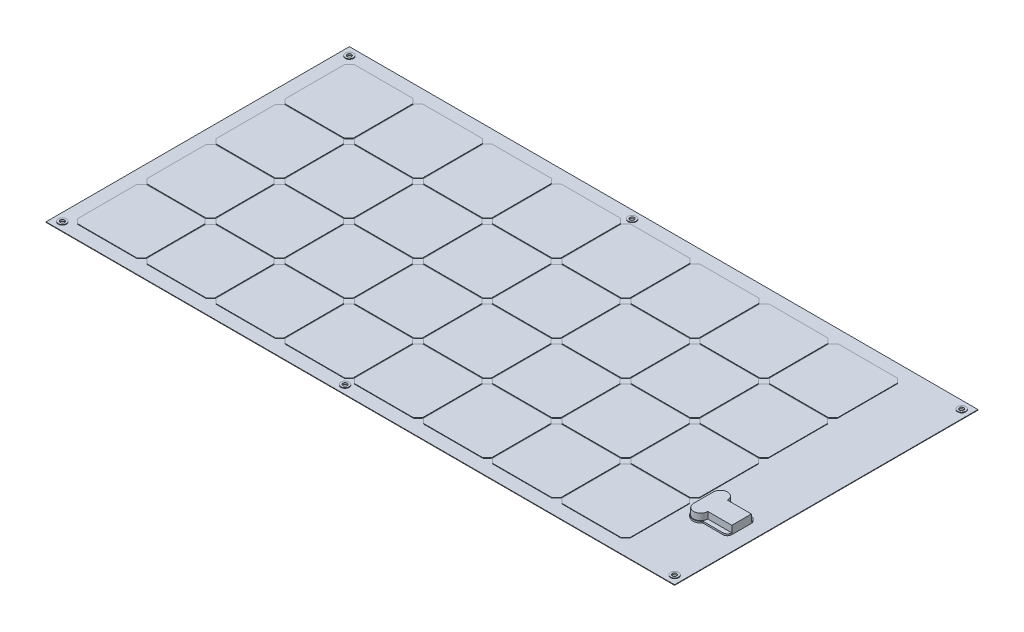
SolidWorks part; units mm, degrees
ref_plane "Front Plane" through (0, 0, 0) normal (0, 0, 1) x (1, 0, 0)
ref_plane "Top Plane" through (0, 0, 0) normal (0, 1, 0) x (1, 0, 0)
ref_plane "Right Plane" through (0, 0, 0) normal (1, 0, 0) x (0, 0, -1)
sketch "Sketch1" plane through (0, 0, 0) normal (0, 1, 0) x (1, 0, 0)
  line L1 (-577, 278.5) -> (577, 278.5)
  line L2 (-577, 278.5) -> (-577, -278.5)
  line L3 (-577, -278.5) -> (577, -278.5)
  line L4 (577, 278.5) -> (577, -278.5)
  line L5 (-577, 278.5) -> (577, -278.5) construction
  line L6 (-577, -278.5) -> (577, 278.5) construction
  point P0 (0, 0)
  dimension "D1" = 557
  dimension "D2" = 1154
extrude "Boss-Extrude1" add sketch "Sketch1" along normal blind 1
sketch "Sketch2" plane through (0, 1, 0) normal (0, 1, 0) x (1, 0, 0)
  line L0 (-577, 0) -> (577, 0) construction
  line L1 (-577, 278.5) -> (-577, -278.5) construction
  line L2 (577, -278.5) -> (577, 278.5) construction
  line L3 (-577, -278.5) -> (577, -278.5) construction
  circle A0 centre (-562, -263.5) radius 4
  circle A1 centre (-43, -263.5) radius 4
  circle A2 centre (562, -263.5) radius 4
  circle A3 centre (562, 263.5) radius 4
  circle A4 centre (-43, 263.5) radius 4
  circle A5 centre (-562, 263.5) radius 4
  dimension "D3" = 8
  dimension "D4" = 8
  dimension "D7" = 8
  dimension "D1" = 15
  dimension "D2" = 15
  dimension "D5" = 519
  dimension "D6" = 15
  dimension "D8" = 15
  dimension "D9" = 15
extrude "Cut-Extrude1" cut sketch "Sketch2" against normal blind 3
sketch "Sketch3" plane through (0, 1, 0) normal (0, 1, 0) x (1, 0, 0)
  line L0 (-552, -136.5) -> (-544, -128.5)
  line L1 (-544, -128.5) -> (-435, -128.5)
  line L2 (-552, -136.5) -> (-552, -245.5)
  line L3 (-544, -253.5) -> (-435, -253.5)
  line L4 (-427, -136.5) -> (-427, -245.5)
  line L5 (-552, -136.5) -> (-427, -136.5) construction
  line L6 (-552, -245.5) -> (-427, -245.5) construction
  line L7 (-435, -128.5) -> (-427, -136.5)
  line L8 (-435, -253.5) -> (-427, -245.5)
  line L9 (-552, -245.5) -> (-544, -253.5)
  line L10 (-544, -128.5) -> (-544, -253.5) construction
  line L11 (-435, -128.5) -> (-435, -253.5) construction
  line L12 (-577, 278.5) -> (-577, -278.5) construction
  line L13 (-577, -278.5) -> (577, -278.5) construction
  line L14 (-552, -9.5) -> (-544, -1.5)
  line L15 (-544, -1.5) -> (-435, -1.5)
  line L16 (-552, -9.5) -> (-552, -118.5)
  line L17 (-544, -126.5) -> (-435, -126.5)
  line L18 (-427, -9.5) -> (-427, -118.5)
  line L19 (-552, -9.5) -> (-427, -9.5) construction
  line L20 (-552, -118.5) -> (-427, -118.5) construction
  line L21 (-435, -1.5) -> (-427, -9.5)
  line L22 (-435, -126.5) -> (-427, -118.5)
  line L23 (-552, -118.5) -> (-544, -126.5)
  line L24 (-544, -1.5) -> (-544, -126.5) construction
  line L25 (-435, -1.5) -> (-435, -126.5) construction
  line L26 (-552, 117.5) -> (-544, 125.5)
  line L27 (-544, 125.5) -> (-435, 125.5)
  line L28 (-552, 117.5) -> (-552, 8.5)
  line L29 (-544, 0.5) -> (-435, 0.5)
  line L30 (-427, 117.5) -> (-427, 8.5)
  line L31 (-552, 117.5) -> (-427, 117.5) construction
  line L32 (-552, 8.5) -> (-427, 8.5) construction
  line L33 (-435, 125.5) -> (-427, 117.5)
  line L34 (-435, 0.5) -> (-427, 8.5)
  line L35 (-552, 8.5) -> (-544, 0.5)
  line L36 (-544, 125.5) -> (-544, 0.5) construction
  line L37 (-435, 125.5) -> (-435, 0.5) construction
  line L38 (-552, 245.5) -> (-544, 253.5)
  line L39 (-544, 253.5) -> (-435, 253.5)
  line L40 (-552, 245.5) -> (-552, 135.5)
  line L41 (-544, 127.5) -> (-435, 127.5)
  line L42 (-427, 245.5) -> (-427, 135.5)
  line L43 (-552, 245.5) -> (-427, 245.5) construction
  line L44 (-552, 135.5) -> (-427, 135.5) construction
  line L45 (-435, 253.5) -> (-427, 245.5)
  line L46 (-435, 127.5) -> (-427, 135.5)
  line L47 (-552, 135.5) -> (-544, 127.5)
  line L48 (-544, 253.5) -> (-544, 127.5) construction
  line L49 (-435, 253.5) -> (-435, 127.5) construction
  line L50 (577, 278.5) -> (-577, 278.5) construction
  line L51 (-426, 278.5) -> (-426, -278.5) construction
  line L52 (-417, 253.5) -> (-417, 127.5) construction
  line L53 (-308, 253.5) -> (-308, 127.5) construction
  line L54 (-300, 135.5) -> (-425, 135.5) construction
  line L55 (-300, 245.5) -> (-425, 245.5) construction
  line L56 (-417, 125.5) -> (-417, 0.5) construction
  line L57 (-308, 125.5) -> (-308, 0.5) construction
  line L58 (-300, 8.5) -> (-425, 8.5) construction
  line L59 (-300, 117.5) -> (-425, 117.5) construction
  line L60 (-417, -1.5) -> (-417, -126.5) construction
  line L61 (-308, -1.5) -> (-308, -126.5) construction
  line L62 (-300, -118.5) -> (-425, -118.5) construction
  line L63 (-300, -9.5) -> (-425, -9.5) construction
  line L64 (-417, -128.5) -> (-417, -253.5) construction
  line L65 (-308, -128.5) -> (-308, -253.5) construction
  line L66 (-300, -245.5) -> (-425, -245.5) construction
  line L67 (-300, -136.5) -> (-425, -136.5) construction
  line L68 (-300, 135.5) -> (-308, 127.5)
  line L69 (-417, 127.5) -> (-425, 135.5)
  line L70 (-417, 253.5) -> (-425, 245.5)
  line L71 (-425, 245.5) -> (-425, 135.5)
  line L72 (-308, 127.5) -> (-417, 127.5)
  line L73 (-300, 245.5) -> (-300, 135.5)
  line L74 (-308, 253.5) -> (-417, 253.5)
  line L75 (-300, 245.5) -> (-308, 253.5)
  line L76 (-300, 8.5) -> (-308, 0.5)
  line L77 (-417, 0.5) -> (-425, 8.5)
  line L78 (-417, 125.5) -> (-425, 117.5)
  line L79 (-425, 117.5) -> (-425, 8.5)
  line L80 (-308, 0.5) -> (-417, 0.5)
  line L81 (-300, 117.5) -> (-300, 8.5)
  line L82 (-308, 125.5) -> (-417, 125.5)
  line L83 (-300, 117.5) -> (-308, 125.5)
  line L84 (-300, -118.5) -> (-308, -126.5)
  line L85 (-417, -126.5) -> (-425, -118.5)
  line L86 (-417, -1.5) -> (-425, -9.5)
  line L87 (-425, -9.5) -> (-425, -118.5)
  line L88 (-308, -126.5) -> (-417, -126.5)
  line L89 (-300, -9.5) -> (-300, -118.5)
  line L90 (-308, -1.5) -> (-417, -1.5)
  line L91 (-300, -9.5) -> (-308, -1.5)
  line L92 (-300, -245.5) -> (-308, -253.5)
  line L93 (-417, -253.5) -> (-425, -245.5)
  line L94 (-417, -128.5) -> (-425, -136.5)
  line L95 (-425, -136.5) -> (-425, -245.5)
  line L96 (-308, -253.5) -> (-417, -253.5)
  line L97 (-300, -136.5) -> (-300, -245.5)
  line L98 (-308, -128.5) -> (-417, -128.5)
  line L99 (-300, -136.5) -> (-308, -128.5)
  line L100 (-299, 278.5) -> (-299, -278.5) construction
  line L101 (-298, -136.5) -> (-173, -136.5) construction
  line L102 (-298, -245.5) -> (-173, -245.5) construction
  line L103 (-290, -128.5) -> (-290, -253.5) construction
  line L104 (-181, -128.5) -> (-181, -253.5) construction
  line L105 (-298, -9.5) -> (-173, -9.5) construction
  line L106 (-298, -118.5) -> (-173, -118.5) construction
  line L107 (-290, -1.5) -> (-290, -126.5) construction
  line L108 (-181, -1.5) -> (-181, -126.5) construction
  line L109 (-298, 117.5) -> (-173, 117.5) construction
  line L110 (-298, 8.5) -> (-173, 8.5) construction
  line L111 (-290, 125.5) -> (-290, 0.5) construction
  line L112 (-181, 125.5) -> (-181, 0.5) construction
  line L113 (-298, 245.5) -> (-173, 245.5) construction
  line L114 (-298, 135.5) -> (-173, 135.5) construction
  line L115 (-290, 253.5) -> (-290, 127.5) construction
  line L116 (-181, 253.5) -> (-181, 127.5) construction
  line L117 (-163, 253.5) -> (-163, 127.5) construction
  line L118 (-54, 253.5) -> (-54, 127.5) construction
  line L119 (-46, 135.5) -> (-171, 135.5) construction
  line L120 (-46, 245.5) -> (-171, 245.5) construction
  line L121 (-163, 125.5) -> (-163, 0.5) construction
  line L122 (-54, 125.5) -> (-54, 0.5) construction
  line L123 (-46, 8.5) -> (-171, 8.5) construction
  line L124 (-46, 117.5) -> (-171, 117.5) construction
  line L125 (-163, -1.5) -> (-163, -126.5) construction
  line L126 (-54, -1.5) -> (-54, -126.5) construction
  line L127 (-46, -118.5) -> (-171, -118.5) construction
  line L128 (-46, -9.5) -> (-171, -9.5) construction
  line L129 (-163, -128.5) -> (-163, -253.5) construction
  line L130 (-54, -128.5) -> (-54, -253.5) construction
  line L131 (-46, -245.5) -> (-171, -245.5) construction
  line L132 (-46, -136.5) -> (-171, -136.5) construction
  line L133 (-298, -136.5) -> (-290, -128.5)
  line L134 (-290, -128.5) -> (-181, -128.5)
  line L135 (-298, -136.5) -> (-298, -245.5)
  line L136 (-290, -253.5) -> (-181, -253.5)
  line L137 (-173, -136.5) -> (-173, -245.5)
  line L138 (-181, -128.5) -> (-173, -136.5)
  line L139 (-181, -253.5) -> (-173, -245.5)
  line L140 (-298, -245.5) -> (-290, -253.5)
  line L141 (-298, -9.5) -> (-290, -1.5)
  line L142 (-290, -1.5) -> (-181, -1.5)
  line L143 (-298, -9.5) -> (-298, -118.5)
  line L144 (-290, -126.5) -> (-181, -126.5)
  line L145 (-173, -9.5) -> (-173, -118.5)
  line L146 (-181, -1.5) -> (-173, -9.5)
  line L147 (-181, -126.5) -> (-173, -118.5)
  line L148 (-298, -118.5) -> (-290, -126.5)
  line L149 (-298, 117.5) -> (-290, 125.5)
  line L150 (-290, 125.5) -> (-181, 125.5)
  line L151 (-298, 117.5) -> (-298, 8.5)
  line L152 (-290, 0.5) -> (-181, 0.5)
  line L153 (-173, 117.5) -> (-173, 8.5)
  line L154 (-181, 125.5) -> (-173, 117.5)
  line L155 (-181, 0.5) -> (-173, 8.5)
  line L156 (-298, 8.5) -> (-290, 0.5)
  line L157 (-298, 245.5) -> (-290, 253.5)
  line L158 (-290, 253.5) -> (-181, 253.5)
  line L159 (-298, 245.5) -> (-298, 135.5)
  line L160 (-290, 127.5) -> (-181, 127.5)
  line L161 (-173, 245.5) -> (-173, 135.5)
  line L162 (-181, 253.5) -> (-173, 245.5)
  line L163 (-181, 127.5) -> (-173, 135.5)
  line L164 (-298, 135.5) -> (-290, 127.5)
  line L165 (-46, 135.5) -> (-54, 127.5)
  line L166 (-163, 127.5) -> (-171, 135.5)
  line L167 (-163, 253.5) -> (-171, 245.5)
  line L168 (-171, 245.5) -> (-171, 135.5)
  line L169 (-54, 127.5) -> (-163, 127.5)
  line L170 (-46, 245.5) -> (-46, 135.5)
  line L171 (-54, 253.5) -> (-163, 253.5)
  line L172 (-46, 245.5) -> (-54, 253.5)
  line L173 (-46, 8.5) -> (-54, 0.5)
  line L174 (-163, 0.5) -> (-171, 8.5)
  line L175 (-163, 125.5) -> (-171, 117.5)
  line L176 (-171, 117.5) -> (-171, 8.5)
  line L177 (-54, 0.5) -> (-163, 0.5)
  line L178 (-46, 117.5) -> (-46, 8.5)
  line L179 (-54, 125.5) -> (-163, 125.5)
  line L180 (-46, 117.5) -> (-54, 125.5)
  line L181 (-46, -118.5) -> (-54, -126.5)
  line L182 (-163, -126.5) -> (-171, -118.5)
  line L183 (-163, -1.5) -> (-171, -9.5)
  line L184 (-171, -9.5) -> (-171, -118.5)
  line L185 (-54, -126.5) -> (-163, -126.5)
  line L186 (-46, -9.5) -> (-46, -118.5)
  line L187 (-54, -1.5) -> (-163, -1.5)
  line L188 (-46, -9.5) -> (-54, -1.5)
  line L189 (-46, -245.5) -> (-54, -253.5)
  line L190 (-163, -253.5) -> (-171, -245.5)
  line L191 (-163, -128.5) -> (-171, -136.5)
  line L192 (-171, -136.5) -> (-171, -245.5)
  line L193 (-54, -253.5) -> (-163, -253.5)
  line L194 (-46, -136.5) -> (-46, -245.5)
  line L195 (-54, -128.5) -> (-163, -128.5)
  line L196 (-46, -136.5) -> (-54, -128.5)
  line L197 (-45, 278.5) -> (-45, -278.5) construction
  line L198 (-44, -136.5) -> (81, -136.5) construction
  line L199 (-44, -245.5) -> (81, -245.5) construction
  line L200 (-36, -128.5) -> (-36, -253.5) construction
  line L201 (73, -128.5) -> (73, -253.5) construction
  line L202 (-44, -9.5) -> (81, -9.5) construction
  line L203 (-44, -118.5) -> (81, -118.5) construction
  line L204 (-36, -1.5) -> (-36, -126.5) construction
  line L205 (73, -1.5) -> (73, -126.5) construction
  line L206 (-44, 117.5) -> (81, 117.5) construction
  line L207 (-44, 8.5) -> (81, 8.5) construction
  line L208 (-36, 125.5) -> (-36, 0.5) construction
  line L209 (73, 125.5) -> (73, 0.5) construction
  line L210 (-44, 245.5) -> (81, 245.5) construction
  line L211 (-44, 135.5) -> (81, 135.5) construction
  line L212 (-36, 253.5) -> (-36, 127.5) construction
  line L213 (73, 253.5) -> (73, 127.5) construction
  line L214 (91, 253.5) -> (91, 127.5) construction
  line L215 (200, 253.5) -> (200, 127.5) construction
  line L216 (208, 135.5) -> (83, 135.5) construction
  line L217 (208, 245.5) -> (83, 245.5) construction
  line L218 (91, 125.5) -> (91, 0.5) construction
  line L219 (200, 125.5) -> (200, 0.5) construction
  line L220 (208, 8.5) -> (83, 8.5) construction
  line L221 (208, 117.5) -> (83, 117.5) construction
  line L222 (91, -1.5) -> (91, -126.5) construction
  line L223 (200, -1.5) -> (200, -126.5) construction
  line L224 (208, -118.5) -> (83, -118.5) construction
  line L225 (208, -9.5) -> (83, -9.5) construction
  line L226 (91, -128.5) -> (91, -253.5) construction
  line L227 (200, -128.5) -> (200, -253.5) construction
  line L228 (208, -245.5) -> (83, -245.5) construction
  line L229 (208, -136.5) -> (83, -136.5) construction
  line L230 (210, -136.5) -> (335, -136.5) construction
  line L231 (210, -245.5) -> (335, -245.5) construction
  line L232 (218, -128.5) -> (218, -253.5) construction
  line L233 (327, -128.5) -> (327, -253.5) construction
  line L234 (210, -9.5) -> (335, -9.5) construction
  line L235 (210, -118.5) -> (335, -118.5) construction
  line L236 (218, -1.5) -> (218, -126.5) construction
  line L237 (327, -1.5) -> (327, -126.5) construction
  line L238 (210, 117.5) -> (335, 117.5) construction
  line L239 (210, 8.5) -> (335, 8.5) construction
  line L240 (218, 125.5) -> (218, 0.5) construction
  line L241 (327, 125.5) -> (327, 0.5) construction
  line L242 (210, 245.5) -> (335, 245.5) construction
  line L243 (210, 135.5) -> (335, 135.5) construction
  line L244 (218, 253.5) -> (218, 127.5) construction
  line L245 (327, 253.5) -> (327, 127.5) construction
  line L246 (345, 253.5) -> (345, 127.5) construction
  line L247 (454, 253.5) -> (454, 127.5) construction
  line L248 (462, 135.5) -> (337, 135.5) construction
  line L249 (462, 245.5) -> (337, 245.5) construction
  line L250 (345, 125.5) -> (345, 0.5) construction
  line L251 (454, 125.5) -> (454, 0.5) construction
  line L252 (462, 8.5) -> (337, 8.5) construction
  line L253 (462, 117.5) -> (337, 117.5) construction
  line L254 (345, -1.5) -> (345, -126.5) construction
  line L255 (454, -1.5) -> (454, -126.5) construction
  line L256 (462, -118.5) -> (337, -118.5) construction
  line L257 (462, -9.5) -> (337, -9.5) construction
  line L258 (345, -128.5) -> (345, -253.5) construction
  line L259 (454, -128.5) -> (454, -253.5) construction
  line L260 (462, -245.5) -> (337, -245.5) construction
  line L261 (462, -136.5) -> (337, -136.5) construction
  line L262 (-44, -136.5) -> (-36, -128.5)
  line L263 (-36, -128.5) -> (73, -128.5)
  line L264 (-44, -136.5) -> (-44, -245.5)
  line L265 (-36, -253.5) -> (73, -253.5)
  line L266 (81, -136.5) -> (81, -245.5)
  line L267 (73, -128.5) -> (81, -136.5)
  line L268 (73, -253.5) -> (81, -245.5)
  line L269 (-44, -245.5) -> (-36, -253.5)
  line L270 (-44, -9.5) -> (-36, -1.5)
  line L271 (-36, -1.5) -> (73, -1.5)
  line L272 (-44, -9.5) -> (-44, -118.5)
  line L273 (-36, -126.5) -> (73, -126.5)
  line L274 (81, -9.5) -> (81, -118.5)
  line L275 (73, -1.5) -> (81, -9.5)
  line L276 (73, -126.5) -> (81, -118.5)
  line L277 (-44, -118.5) -> (-36, -126.5)
  line L278 (-44, 117.5) -> (-36, 125.5)
  line L279 (-36, 125.5) -> (73, 125.5)
  line L280 (-44, 117.5) -> (-44, 8.5)
  line L281 (-36, 0.5) -> (73, 0.5)
  line L282 (81, 117.5) -> (81, 8.5)
  line L283 (73, 125.5) -> (81, 117.5)
  line L284 (73, 0.5) -> (81, 8.5)
  line L285 (-44, 8.5) -> (-36, 0.5)
  line L286 (-44, 245.5) -> (-36, 253.5)
  line L287 (-36, 253.5) -> (73, 253.5)
  line L288 (-44, 245.5) -> (-44, 135.5)
  line L289 (-36, 127.5) -> (73, 127.5)
  line L290 (81, 245.5) -> (81, 135.5)
  line L291 (73, 253.5) -> (81, 245.5)
  line L292 (73, 127.5) -> (81, 135.5)
  line L293 (-44, 135.5) -> (-36, 127.5)
  line L294 (208, 135.5) -> (200, 127.5)
  line L295 (91, 127.5) -> (83, 135.5)
  line L296 (91, 253.5) -> (83, 245.5)
  line L297 (83, 245.5) -> (83, 135.5)
  line L298 (200, 127.5) -> (91, 127.5)
  line L299 (208, 245.5) -> (208, 135.5)
  line L300 (200, 253.5) -> (91, 253.5)
  line L301 (208, 245.5) -> (200, 253.5)
  line L302 (208, 8.5) -> (200, 0.5)
  line L303 (91, 0.5) -> (83, 8.5)
  line L304 (91, 125.5) -> (83, 117.5)
  line L305 (83, 117.5) -> (83, 8.5)
  line L306 (200, 0.5) -> (91, 0.5)
  line L307 (208, 117.5) -> (208, 8.5)
  line L308 (200, 125.5) -> (91, 125.5)
  line L309 (208, 117.5) -> (200, 125.5)
  line L310 (208, -118.5) -> (200, -126.5)
  line L311 (91, -126.5) -> (83, -118.5)
  line L312 (91, -1.5) -> (83, -9.5)
  line L313 (83, -9.5) -> (83, -118.5)
  line L314 (200, -126.5) -> (91, -126.5)
  line L315 (208, -9.5) -> (208, -118.5)
  line L316 (200, -1.5) -> (91, -1.5)
  line L317 (208, -9.5) -> (200, -1.5)
  line L318 (208, -245.5) -> (200, -253.5)
  line L319 (91, -253.5) -> (83, -245.5)
  line L320 (91, -128.5) -> (83, -136.5)
  line L321 (83, -136.5) -> (83, -245.5)
  line L322 (200, -253.5) -> (91, -253.5)
  line L323 (208, -136.5) -> (208, -245.5)
  line L324 (200, -128.5) -> (91, -128.5)
  line L325 (208, -136.5) -> (200, -128.5)
  line L326 (210, -136.5) -> (218, -128.5)
  line L327 (218, -128.5) -> (327, -128.5)
  line L328 (210, -136.5) -> (210, -245.5)
  line L329 (218, -253.5) -> (327, -253.5)
  line L330 (335, -136.5) -> (335, -245.5)
  line L331 (327, -128.5) -> (335, -136.5)
  line L332 (327, -253.5) -> (335, -245.5)
  line L333 (210, -245.5) -> (218, -253.5)
  line L334 (210, -9.5) -> (218, -1.5)
  line L335 (218, -1.5) -> (327, -1.5)
  line L336 (210, -9.5) -> (210, -118.5)
  line L337 (218, -126.5) -> (327, -126.5)
  line L338 (335, -9.5) -> (335, -118.5)
  line L339 (327, -1.5) -> (335, -9.5)
  line L340 (327, -126.5) -> (335, -118.5)
  line L341 (210, -118.5) -> (218, -126.5)
  line L342 (210, 117.5) -> (218, 125.5)
  line L343 (218, 125.5) -> (327, 125.5)
  line L344 (210, 117.5) -> (210, 8.5)
  line L345 (218, 0.5) -> (327, 0.5)
  line L346 (335, 117.5) -> (335, 8.5)
  line L347 (327, 125.5) -> (335, 117.5)
  line L348 (327, 0.5) -> (335, 8.5)
  line L349 (210, 8.5) -> (218, 0.5)
  line L350 (210, 245.5) -> (218, 253.5)
  line L351 (218, 253.5) -> (327, 253.5)
  line L352 (210, 245.5) -> (210, 135.5)
  line L353 (218, 127.5) -> (327, 127.5)
  line L354 (335, 245.5) -> (335, 135.5)
  line L355 (327, 253.5) -> (335, 245.5)
  line L356 (327, 127.5) -> (335, 135.5)
  line L357 (210, 135.5) -> (218, 127.5)
  line L358 (462, 135.5) -> (454, 127.5)
  line L359 (345, 127.5) -> (337, 135.5)
  line L360 (345, 253.5) -> (337, 245.5)
  line L361 (337, 245.5) -> (337, 135.5)
  line L362 (454, 127.5) -> (345, 127.5)
  line L363 (462, 245.5) -> (462, 135.5)
  line L364 (454, 253.5) -> (345, 253.5)
  line L365 (462, 245.5) -> (454, 253.5)
  line L366 (462, 8.5) -> (454, 0.5)
  line L367 (345, 0.5) -> (337, 8.5)
  line L368 (345, 125.5) -> (337, 117.5)
  line L369 (337, 117.5) -> (337, 8.5)
  line L370 (454, 0.5) -> (345, 0.5)
  line L371 (462, 117.5) -> (462, 8.5)
  line L372 (454, 125.5) -> (345, 125.5)
  line L373 (462, 117.5) -> (454, 125.5)
  line L374 (462, -118.5) -> (454, -126.5)
  line L375 (345, -126.5) -> (337, -118.5)
  line L376 (345, -1.5) -> (337, -9.5)
  line L377 (337, -9.5) -> (337, -118.5)
  line L378 (454, -126.5) -> (345, -126.5)
  line L379 (462, -9.5) -> (462, -118.5)
  line L380 (454, -1.5) -> (345, -1.5)
  line L381 (462, -9.5) -> (454, -1.5)
  line L382 (462, -245.5) -> (454, -253.5)
  line L383 (345, -253.5) -> (337, -245.5)
  line L384 (345, -128.5) -> (337, -136.5)
  line L385 (337, -136.5) -> (337, -245.5)
  line L386 (454, -253.5) -> (345, -253.5)
  line L387 (462, -136.5) -> (462, -245.5)
  line L388 (454, -128.5) -> (345, -128.5)
  line L389 (462, -136.5) -> (454, -128.5)
  dimension "D1" = 135
  dimension "D2" = 135
  dimension "D3" = 135
  dimension "D4" = 135
  dimension "D5" = 109
  dimension "D6" = 109
  dimension "D7" = 25
  dimension "D8" = 25
  dimension "D9" = 125
  dimension "D10" = 135
  dimension "D11" = 135
  dimension "D12" = 135
  dimension "D13" = 135
  dimension "D14" = 125
  dimension "D15" = 25
  dimension "D16" = 109
  dimension "D17" = 2
  dimension "D18" = 125
  dimension "D19" = 135
  dimension "D20" = 135
  dimension "D21" = 135
  dimension "D22" = 135
  dimension "D23" = 125
  dimension "D24" = 25
  dimension "D25" = 125
  dimension "D26" = 109
  dimension "D27" = 2
  dimension "D28" = 135
  dimension "D29" = 135
  dimension "D30" = 135
  dimension "D31" = 135
  dimension "D32" = 125
  dimension "D33" = 25
  dimension "D34" = 25
  dimension "D35" = 109
  dimension "D36" = 2
  dimension "D37" = 1
  dimension "D38" = 1
  dimension "D39" = 1
extrude "Boss-Extrude2" add sketch "Sketch3" along normal blind 1
sketch "Sketch4" plane through (0, 1, 0) normal (0, 1, 0) x (1, 0, 0)
  line L0 (-577, 0) -> (577, 0) construction
  line L1 (-577, 278.5) -> (-577, -278.5) construction
  line L2 (577, -278.5) -> (577, 278.5) construction
  circle A0 centre (-562, -263.5) radius 4
  circle A1 centre (-562, -263.5) radius 7.5
  circle A2 centre (-43, -263.5) radius 4
  circle A3 centre (-43, -263.5) radius 7.5
  circle A4 centre (562, -263.5) radius 4
  circle A5 centre (562, -263.5) radius 7.5
  circle A6 centre (562, 263.5) radius 7.5
  circle A7 centre (562, 263.5) radius 4
  circle A8 centre (-43, 263.5) radius 7.5
  circle A9 centre (-43, 263.5) radius 4
  circle A10 centre (-562, 263.5) radius 7.5
  circle A11 centre (-562, 263.5) radius 4
  dimension "D1" = 15
  dimension "D2" = 8
  dimension "D3" = 15
  dimension "D4" = 8
  dimension "D5" = 15
  dimension "D6" = 8
extrude "Boss-Extrude3" add sketch "Sketch4" along normal blind 1 and the other way blind 2
sketch "Sketch5" plane through (0, 1, 0) normal (0, 1, 0) x (1, 0, 0)
  line L0 (577, -278.5) -> (577, 278.5) construction
  line L2 (478.0065, -111.4672) -> (478.0065, -145.5328)
  line L4 (550, -110.5) -> (550, -146.5)
  line L5 (478.0065, -128.5) -> (550, -128.5) construction
  line L7 (-577, -278.5) -> (577, -278.5) construction
  line L8 (542, -102.5) -> (505.031, -102.5)
  line L9 (542, -154.5) -> (505.031, -154.5)
  arc A0 (505.031, -102.5) -> (478.0065, -111.4672) centre (493.0065, -111.4672) ccw
  arc A1 (478.0065, -145.5328) -> (505.031, -154.5) centre (493.0065, -145.5328) ccw
  arc A2 (542, -154.5) -> (550, -146.5) centre (542, -146.5) ccw
  arc A3 (550, -110.5) -> (542, -102.5) centre (542, -110.5) ccw
  dimension "D5" = 30
  dimension "D6" = 30
  dimension "D7" = 16
  dimension "D8" = 16
  dimension "D1" = 36
  dimension "D2" = 72
  dimension "D3" = 27
  dimension "D4" = 8
  dimension "D9" = 8
  dimension "D10" = 124
  dimension "D11" = 34.0656
  dimension "D12" = 15
  dimension "D13" = 15
extrude "Boss-Extrude4" add sketch "Sketch5" along normal blind 3
sketch "Sketch6" plane through (0, 4, 0) normal (0, 1, 0) x (1, 0, 0)
  line L0 (550, -146.5) -> (550, -110.5) construction
  line L1 (506, -110.5) -> (550, -110.5)
  line L3 (506, -146.5) -> (550, -146.5)
  line L4 (550, -110.5) -> (550, -146.5)
  line L5 (506, -110.5) -> (550, -146.5) construction
  line L6 (506, -146.5) -> (550, -110.5) construction
  line L7 (478.0065, -111.4672) -> (478.0065, -145.5328) construction
  line L8 (478.0065, -128.5) -> (550, -128.5) construction
  line L13 (480, -146.5) -> (480, -110.5)
  arc A0 (506, -110.5) -> (480, -110.5) centre (493, -110.5) ccw
  arc A1 (480, -146.5) -> (506, -146.5) centre (493, -146.5) ccw
  point P0 (528, -128.5)
  dimension "D4" = 13
  dimension "D5" = 13
  dimension "D1" = 44
  dimension "D2" = 36
  dimension "D3" = 26
  dimension "D6" = 18
  dimension "D7" = 36
  dimension "D8" = 70
extrude "Boss-Extrude5" add sketch "Sketch6" along normal blind 12
